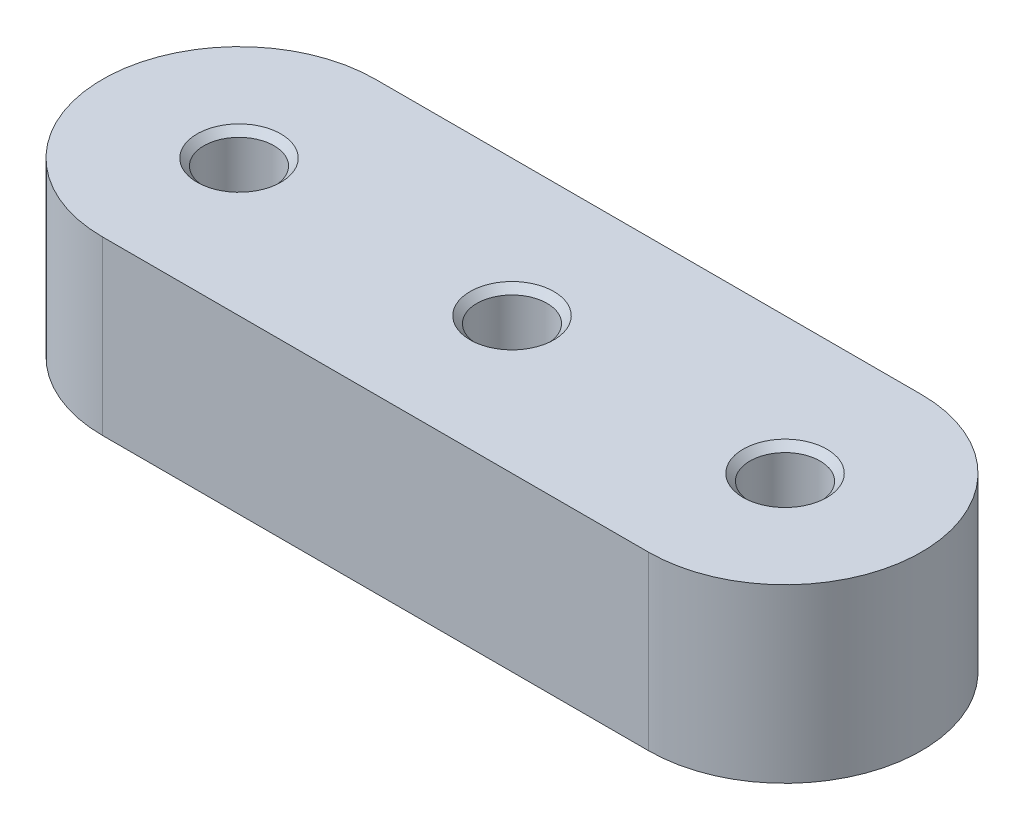
SolidWorks part; units mm, degrees
material "6061-T6 (SS)"
ref_plane "Front" through (0, 0, 0) normal (0, 0, 1) x (1, 0, 0)
ref_plane "Top" through (0, 0, 0) normal (0, 1, 0) x (1, 0, 0)
ref_plane "Right" through (0, 0, 0) normal (1, 0, 0) x (0, 0, -1)
sketch "Sketch1" plane through (0, 0, 0) normal (0, 1, 0) x (1, 0, 0)
  line L0 (-25.4, 12.7) -> (25.4, -12.7) construction
  line L1 (-25.4, 12.7) -> (25.4, 12.7)
  line L2 (-25.4, 12.7) -> (-25.4, -12.7) construction
  line L3 (-25.4, -12.7) -> (25.4, -12.7)
  line L4 (25.4, 12.7) -> (25.4, -12.7) construction
  arc A0 (-25.4, 12.7) -> (-25.4, -12.7) centre (-25.4, 0) ccw
  arc A1 (25.4, -12.7) -> (25.4, 12.7) centre (25.4, 0) ccw
  point P4 (0, 0)
  dimension "D1" = 50.8
  dimension "D2" = 25.4
extrude "Extrude1" add sketch "Sketch1" against normal blind 16
hole_wizard "1/4 Clearance Hole1" positions "Sketch3" profile "Sketch2" hole size "1/4" standard "Ansi Inch" end condition up to next
sketch "Sketch3" plane through (0, 0, 0) normal (0, 1, 0) x (-1, 0, 0)
  line L0 (25.4, -12.7) -> (-25.4, 12.7) construction
  point P0 (0, 0)
  point P3 (0, 0)
  point P4 (25.4, 0)
  point P7 (-25.4, 0)
sketch "Sketch2" plane through (0, 0, 0) normal (1, 0, 0) x (0, 0, 1)
  line L0 (0, 0) -> (0, 16)
  line L1 (0, 16) -> (3.8989, 16)
  line L2 (3.2639, 15.365) -> (3.2639, 0.635)
  line L3 (3.2639, 0.635) -> (3.8989, 0)
  line L5 (3.8989, 0) -> (0, 0)
  line L6 (-3.2639, 0.635) -> (-3.8989, 0) construction
  line L7 (3.8989, 16) -> (3.2639, 15.365)
  line L8 (-3.8989, 16) -> (-3.2639, 15.365) construction
  line L11 (0, -6.35) -> (0, 107.95) construction
  dimension "Thru Hole Dia." = 6.5278
  dimension "Thru Hole Depth" = 16
  dimension "Near C'Sink Dia." = 7.7978
  dimension "Near C'Sink Angle" = 90
  dimension "Far C'Sink Dia." = 7.7978
  dimension "Far C'Sink Angle" = 90
